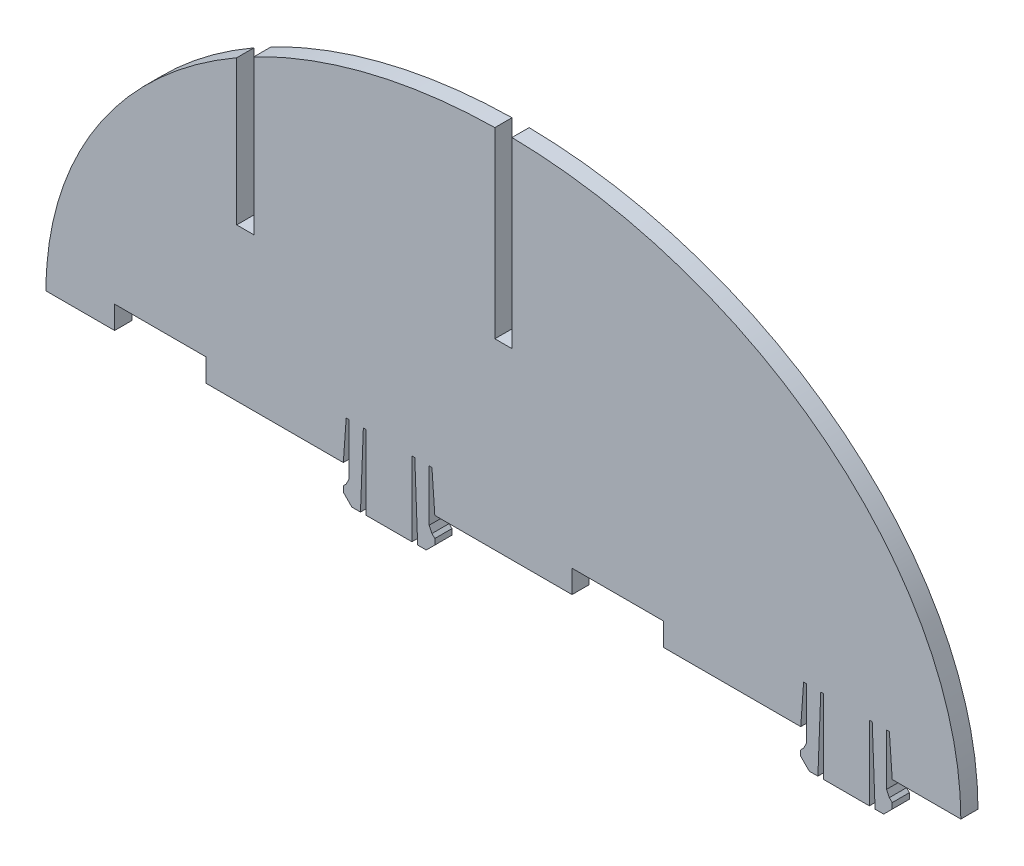
SolidWorks part; units mm, degrees
ref_plane "Front Plane" through (0, 0, 0) normal (0, 0, 1) x (1, 0, 0)
ref_plane "Top Plane" through (0, 0, 0) normal (0, 1, 0) x (1, 0, 0)
ref_plane "Right Plane" through (0, 0, 0) normal (1, 0, 0) x (0, 0, -1)
sketch "Sketch1" plane through (0, 0, 0) normal (0, 0, 1) x (1, 0, 0)
  line L0 (-80, 41.2311) -> (-28, 41.2311)
  line L1 (68, 41.2311) -> (80, 41.2311)
  line L2 (-12, 41.2311) -> (52, 41.2311)
  line L3 (-12, 41.2311) -> (-12.5, 48.2332)
  line L4 (-12.5, 48.2332) -> (-13, 48.2332)
  line L5 (-13, 48.2332) -> (-13, 39.2332)
  line L6 (-13, 39.2332) -> (-12.5, 38.2332)
  line L7 (-12.5, 38.2332) -> (-12, 37.7332)
  line L8 (-12, 37.7332) -> (-12, 36.7332)
  line L9 (-12, 36.7332) -> (-13.5, 35.2332)
  line L10 (-13.5, 35.2332) -> (-15, 35.2332)
  line L11 (-15, 35.2332) -> (-15.5, 48.2332)
  line L12 (-15.5, 48.2332) -> (-16, 48.2332)
  line L13 (-16, 48.2332) -> (-16, 35.2332)
  line L14 (-20, 41.2311) -> (-20, 35.4924) construction
  line L15 (-24, 48.2332) -> (-24, 35.2332)
  line L16 (-24.5, 48.2332) -> (-24, 48.2332)
  line L17 (-25, 35.2332) -> (-24.5, 48.2332)
  line L18 (-26.5, 35.2332) -> (-25, 35.2332)
  line L19 (-28, 36.7332) -> (-26.5, 35.2332)
  line L20 (-28, 37.7332) -> (-28, 36.7332)
  line L21 (-27.5, 38.2332) -> (-28, 37.7332)
  line L22 (-27, 39.2332) -> (-27.5, 38.2332)
  line L23 (-27, 48.2332) -> (-27, 39.2332)
  line L24 (-27.5, 48.2332) -> (-27, 48.2332)
  line L25 (-28, 41.2311) -> (-27.5, 48.2332)
  line L26 (-16, 35.2332) -> (-24, 35.2332)
  line L27 (68, 41.2311) -> (67.5, 48.2332)
  line L28 (67.5, 48.2332) -> (67, 48.2332)
  line L29 (67, 48.2332) -> (67, 39.2332)
  line L30 (67, 39.2332) -> (67.5, 38.2332)
  line L31 (67.5, 38.2332) -> (68, 37.7332)
  line L32 (68, 37.7332) -> (68, 36.7332)
  line L33 (68, 36.7332) -> (66.5, 35.2332)
  line L34 (66.5, 35.2332) -> (65, 35.2332)
  line L35 (65, 35.2332) -> (64.5, 48.2332)
  line L36 (64.5, 48.2332) -> (64, 48.2332)
  line L37 (64, 48.2332) -> (64, 35.2332)
  line L38 (60, 41.2311) -> (60, 35.4924) construction
  line L39 (56, 48.2332) -> (56, 35.2332)
  line L40 (55.5, 48.2332) -> (56, 48.2332)
  line L41 (55, 35.2332) -> (55.5, 48.2332)
  line L42 (53.5, 35.2332) -> (55, 35.2332)
  line L43 (52, 36.7332) -> (53.5, 35.2332)
  line L44 (52, 37.7332) -> (52, 36.7332)
  line L45 (52.5, 38.2332) -> (52, 37.7332)
  line L46 (53, 39.2332) -> (52.5, 38.2332)
  line L47 (53, 48.2332) -> (53, 39.2332)
  line L48 (52.5, 48.2332) -> (53, 48.2332)
  line L49 (52, 41.2311) -> (52.5, 48.2332)
  line L50 (64, 35.2332) -> (56, 35.2332)
  line L51 (-80, 41.2311) -> (0, 0) construction
  line L52 (0, 0) -> (80, 41.2311) construction
  ellipse E0 centre (0, 41.2311) end of major axis (80, 41.2311) minor radius 63.9989 (0, 105.23) -> (-80, 41.2311) ccw
  ellipse E1 centre (0, 41.2311) end of major axis (80, 41.2311) minor radius 63.9989 (0, 105.23) -> (80, 41.2311) cw
  point P10 (60, 41.2311)
  point P11 (68, 41.2311)
  point P12 (-20, 41.2311)
  point P13 (-12, 41.2311)
  point P14 (-28, 41.2311)
  point P15 (-28, 41.2311)
  point P40 (52, 41.2311)
  point P41 (52, 41.2311)
  dimension "D2" = 52
  dimension "D3" = 64
  dimension "D4" = 12
  dimension "D5" = 63.9989
  dimension "D6" = 8
  dimension "D7" = 0.5
  dimension "D8" = 9
  dimension "D9" = 0.5
  dimension "D10" = 1
  dimension "D11" = 0.5
  dimension "D12" = 0.5
  dimension "D13" = 1
  dimension "D14" = 1.5
  dimension "D15" = 1.5
  dimension "D16" = 0.5
  dimension "D17" = 0.5
  dimension "D18" = 13
  dimension "D19" = 7.0022
  dimension "D20" = 0.5
  dimension "D21" = 1.5
  dimension "D22" = 13
  dimension "D23" = 8
  dimension "D24" = 8
  dimension "D25" = 0.5
  dimension "D26" = 9
  dimension "D27" = 0.5
  dimension "D28" = 1
  dimension "D29" = 0.5
  dimension "D30" = 0.5
  dimension "D31" = 1
  dimension "D32" = 1.5
  dimension "D33" = 1.5
  dimension "D34" = 0.5
  dimension "D35" = 0.5
  dimension "D36" = 13
  dimension "D37" = 7.0022
  dimension "D38" = 0.5
  dimension "D39" = 1.5
  dimension "D40" = 13
  dimension "D41" = 8
  dimension "D42" = 63.9989
  dimension "D43" = 80
  dimension "D44" = 41.2311
  dimension "D45" = 90
  dimension "D46" = 90
extrude "Boss-Extrude1" add sketch "Sketch1" along normal blind 3
sketch "Sketch8" plane through (0, 0, 3) normal (0, 0, 1) x (1, 0, 0)
  line L0 (-68, 41.2311) -> (-68, 45.2311)
  line L1 (-80, 41.2311) -> (-28, 41.2311) construction
  line L2 (-68, 45.2311) -> (-52, 45.2311)
  line L3 (-52, 45.2311) -> (-52, 41.2311)
  dimension "D1" = 16
  dimension "D2" = 4
  dimension "D3" = 12
extrude "Cut-Extrude1" cut sketch "Sketch8" against normal blind 3 and the other way through all flip side to cut
sketch "Sketch9" plane through (0, 0, 3) normal (0, 0, 1) x (1, 0, 0)
  line L0 (12, 45.2311) -> (12, 41.2311)
  line L2 (-12, 41.2311) -> (52, 41.2311) construction
  line L3 (12, 45.2311) -> (28, 45.2311)
  line L4 (28, 45.2311) -> (28, 41.2311)
  dimension "D1" = 16
  dimension "D2" = 4
  dimension "D3" = 40
extrude "Cut-Extrude2" cut sketch "Sketch9" against normal blind 3 and the other way through all flip side to cut
sketch "Sketch10" plane through (0, 0, 3) normal (0, 0, 1) x (1, 0, 0)
  line L0 (-1.5, 105.2187) -> (-1.5, 73.231)
  line L1 (-1.5, 73.231) -> (1.5, 73.231)
  line L2 (1.5, 73.231) -> (1.5, 105.2187)
  ellipse E0 centre (0, 41.2311) end of major axis (80, 41.2311) minor radius 63.9989 (80, 41.2311) -> (-80, 41.2311) ccw construction
  dimension "D1" = 31.9877
  dimension "D2" = 3
  dimension "D3" = 31.9877
extrude "Cut-Extrude3" cut sketch "Sketch10" against normal blind 3 and the other way through all
sketch "Sketch11" plane through (0, 0, 3) normal (0, 0, 1) x (1, 0, 0)
  line L0 (-46.6484, 67.9042) -> (-43.6484, 67.9042)
  line L5 (-46.6484, 67.9042) -> (-46.6484, 93.2236)
  line L6 (-43.6484, 67.9042) -> (-43.6484, 94.8649)
  ellipse E1 centre (0, 41.2311) end of major axis (80, 41.2311) minor radius 63.9989 (-1.5, 105.2187) -> (-80, 41.2311) ccw construction
  dimension "D1" = 25.3194
  dimension "D2" = 26.9607
  dimension "D3" = 3
extrude "Cut-Extrude4" cut sketch "Sketch11" against normal blind 3 and the other way through all
sketch "Sketch12" plane through (0, 0, 3) normal (0, 0, 1) x (1, 0, 0)
  text T0 "HZ3" font "Century Gothic" height in points 20
  dimension "D1" = 49.8712
  dimension "D2" = 12.8324
